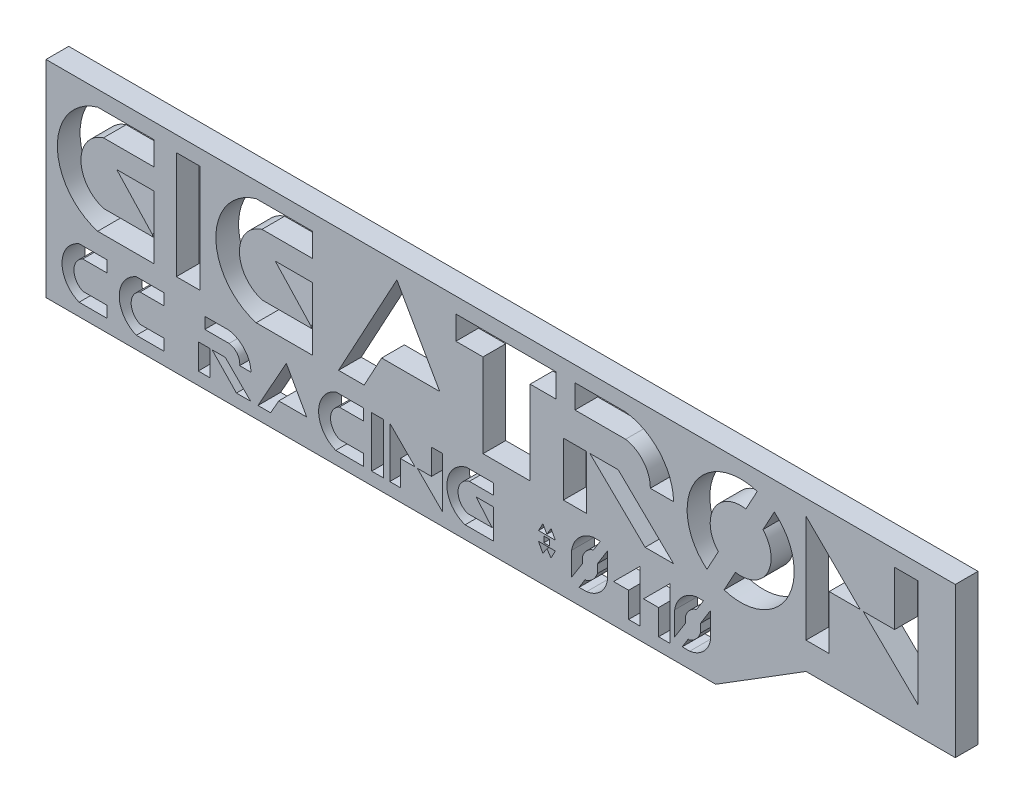
SolidWorks part; units mm, degrees
ref_plane "Front Plane" through (0, 0, 0) normal (0, 0, 1) x (1, 0, 0)
ref_plane "Top Plane" through (0, 0, 0) normal (0, 1, 0) x (1, 0, 0)
ref_plane "Right Plane" through (0, 0, 0) normal (1, 0, 0) x (0, 0, -1)
sketch "Sketch1" plane through (0, 0, 0) normal (0, 0, 1) x (1, 0, 0)
  line L0 (97.5, 52.5) -> (487.5, 52.5) construction
  line L1 (97.7035, 32.2566) -> (489.0368, 32.2566) construction
  line L2 (6.0369, 7.5244) -> (6.0369, 6.2034)
  line L3 (3.2137, 6.2034) -> (6.0369, 6.2034)
  line L4 (6.0369, 5.0366) -> (6.0369, 1.5154)
  line L5 (6.0369, 1.5154) -> (2.8899, 1.5154)
  line L6 (3.2137, 2.7845) -> (5.9435, 2.7845)
  line L7 (3.9568, 5.0366) -> (5.9435, 2.896)
  line L8 (5.9435, 2.7845) -> (5.9435, 2.896)
  line L9 (3.9568, 5.0366) -> (6.0369, 5.0366)
  line L10 (2.8899, 7.5244) -> (6.0369, 7.5244)
  line L11 (7.2903, 7.5244) -> (7.2903, 1.5154)
  line L12 (7.2903, 1.5154) -> (8.6142, 1.5154)
  line L13 (8.6142, 1.5154) -> (8.6142, 7.5244)
  line L14 (8.6142, 7.5244) -> (7.2903, 7.5244)
  line L15 (12.0783, 2.7845) -> (14.8081, 2.7845)
  line L16 (11.7545, 7.5244) -> (14.9015, 7.5244)
  line L17 (14.9015, 7.5244) -> (14.9015, 6.2034)
  line L18 (12.8214, 5.0366) -> (14.9015, 5.0366)
  line L19 (12.0783, 6.2034) -> (14.9015, 6.2034)
  line L20 (14.9015, 1.5154) -> (11.7545, 1.5154)
  line L21 (14.8081, 2.7845) -> (14.8081, 2.896)
  line L22 (14.9015, 5.0366) -> (14.9015, 1.5154)
  line L23 (12.8214, 5.0366) -> (14.8081, 2.896)
  line L24 (16.36, 1.5154) -> (19.6219, 7.5244)
  line L25 (19.6219, 7.5244) -> (22.0222, 3.3181)
  line L26 (22.0222, 3.3181) -> (18.7718, 3.3181)
  line L27 (18.7718, 3.3181) -> (17.7932, 1.5154)
  line L28 (17.7932, 1.5154) -> (16.36, 1.5154)
  line L29 (22.9223, 6.2034) -> (22.9223, 7.5244)
  line L30 (22.9223, 7.5244) -> (28.5231, 7.5244)
  line L31 (28.5231, 7.5244) -> (28.5231, 6.2034)
  line L32 (28.5231, 6.2034) -> (27.0784, 6.2034)
  line L33 (27.0784, 6.2034) -> (27.0784, 1.5154)
  line L34 (27.0784, 1.5154) -> (24.4392, 1.5154)
  line L35 (24.4392, 1.5154) -> (24.4392, 6.2034)
  line L36 (24.4392, 6.2034) -> (22.9223, 6.2034)
  line L37 (28.9324, 1.5154) -> (28.9324, 4.5199)
  line L38 (0, 8.3917) -> (50.8536, 8.3917)
  line L39 (0, 8.3917) -> (0, -3.145)
  line L40 (0, -3.145) -> (37.4561, -3.145)
  line L41 (50.8536, 8.3917) -> (50.8536, 0)
  line L42 (28.9324, 4.5199) -> (30.2353, 4.5199)
  line L43 (30.2353, 4.5199) -> (30.2353, 1.5154)
  line L44 (30.2353, 1.5154) -> (28.9324, 1.5154)
  line L45 (30.4133, 4.5199) -> (33.506, 1.5154)
  line L46 (33.506, 1.5154) -> (35.0989, 1.5154)
  line L47 (35.0989, 1.5154) -> (32.0062, 4.5199)
  line L48 (32.0062, 4.5199) -> (30.4133, 4.5199)
  line L49 (29.5839, 7.5244) -> (29.5839, 6.2034)
  line L50 (29.5839, 6.2034) -> (32.4138, 6.2034)
  line L51 (32.4138, 6.2034) -> (32.4138, 7.5244) construction
  line L52 (32.4138, 7.5244) -> (29.5839, 7.5244)
  line L53 (33.7966, 4.5199) -> (35.0992, 4.5199)
  line L54 (48.7766, 1.5154) -> (45.7105, 4.509)
  line L55 (45.7105, 4.509) -> (47.4627, 4.509)
  line L56 (47.4627, 4.509) -> (47.4627, 7.5244)
  line L57 (47.4627, 7.5244) -> (48.7766, 7.5244)
  line L58 (48.7766, 7.5244) -> (48.7766, 1.5154)
  line L59 (42.5034, 7.5244) -> (42.5034, 1.5154)
  line L60 (42.5034, 1.5154) -> (43.799, 1.5154)
  line L61 (43.799, 1.5154) -> (43.799, 4.5199)
  line L62 (43.799, 4.5199) -> (45.5406, 4.5199)
  line L63 (45.5406, 4.5199) -> (42.5034, 7.5244)
  line L64 (37.4561, -3.145) -> (42.5034, 0)
  line L65 (42.5034, 0) -> (50.8536, 0)
  line L66 (1.8512, 0.3925) -> (3.4007, 0.3925)
  line L67 (3.4007, 0.3925) -> (3.4007, -0.2437)
  line L68 (3.4007, -0.2437) -> (2.0566, -0.2437)
  line L69 (2.0638, -1.8089) -> (3.4007, -1.8089)
  line L70 (3.4007, -1.8089) -> (3.4007, -2.4417)
  line L71 (3.4007, -2.4417) -> (1.8512, -2.4417)
  line L72 (6.6011, -1.8089) -> (6.6011, -2.4417)
  line L73 (5.0516, 0.3925) -> (6.6011, 0.3925)
  line L74 (6.6011, -2.4417) -> (5.0516, -2.4417)
  line L75 (5.2642, -1.8089) -> (6.6011, -1.8089)
  line L76 (6.6011, -0.2437) -> (5.257, -0.2437)
  line L77 (6.6011, 0.3925) -> (6.6011, -0.2437)
  line L78 (17.7517, -0.2437) -> (16.4076, -0.2437)
  line L79 (16.4148, -1.8089) -> (17.7517, -1.8089)
  line L80 (17.7517, -2.4417) -> (16.2022, -2.4417)
  line L81 (16.2022, 0.3925) -> (17.7517, 0.3925)
  line L82 (17.7517, -1.8089) -> (17.7517, -2.4417)
  line L83 (17.7517, 0.3925) -> (17.7517, -0.2437)
  line L84 (30.0042, -1.728) -> (30.0042, -0.6842)
  line L85 (29.3957, -2.2683) -> (29.3957, -0.6842)
  line L86 (30.8351, -0.061) -> (30.8351, -1.0945)
  line L87 (31.4055, 0.5528) -> (31.4055, -1.0945)
  line L88 (29.3957, -2.2683) -> (30.2353, -2.2683)
  line L89 (30.5998, 0.5528) -> (31.4055, 0.5528)
  line L90 (30.8351, -0.061) -> (30.5998, -0.061)
  line L91 (30.0042, -1.728) -> (30.2353, -1.728)
  line L92 (35.1615, -2.2683) -> (35.1615, -0.6842)
  line L93 (35.1615, -2.2683) -> (36.0011, -2.2683)
  line L94 (36.6009, -0.061) -> (36.3656, -0.061)
  line L95 (36.3656, 0.5528) -> (37.1713, 0.5528)
  line L96 (36.6009, -0.061) -> (36.6009, -1.0945)
  line L97 (37.1713, 0.5528) -> (37.1713, -1.0945)
  line L98 (35.77, -1.728) -> (35.77, -0.6842)
  line L99 (35.77, -1.728) -> (36.0011, -1.728)
  line L100 (31.7414, -1.0246) -> (33.2093, 0.4432)
  line L101 (33.2093, 0.4432) -> (33.2093, -2.4417)
  line L102 (33.2093, -2.4417) -> (32.583, -2.4417)
  line L103 (32.583, -2.4417) -> (32.583, -1.0246)
  line L104 (32.583, -1.0246) -> (31.7414, -1.0246)
  line L105 (34.8857, 0.4432) -> (34.8857, -2.4417)
  line L106 (34.8857, -2.4417) -> (34.2594, -2.4417)
  line L107 (34.2594, -1.0246) -> (33.4178, -1.0246)
  line L108 (33.4178, -1.0246) -> (34.8857, 0.4432)
  line L109 (34.2594, -2.4417) -> (34.2594, -1.0246)
  line L110 (27.5415, -1.1748) -> (28.4841, -1.1748)
  line L111 (28.4841, -1.1748) -> (28.2445, -1.6381)
  line L112 (28.2445, -1.6381) -> (28.0128, -1.2946)
  line L113 (28.0128, -1.2946) -> (27.7891, -1.6381)
  line L114 (27.7891, -1.6381) -> (27.5415, -1.1748)
  line L115 (27.5415, -0.6528) -> (27.7891, -0.204)
  line L116 (27.845, -0.7682) -> (28.1646, -0.7682)
  line L117 (27.845, -0.7682) -> (27.845, -1.0945)
  line L118 (27.845, -1.0945) -> (28.1646, -1.0945)
  line L119 (28.1646, -0.7682) -> (28.1646, -1.0945)
  line L120 (27.7891, -0.204) -> (28.0128, -0.6012)
  line L121 (28.0128, -0.6012) -> (28.2445, -0.204)
  line L122 (28.2445, -0.204) -> (28.4841, -0.6528)
  line L123 (28.4841, -0.6528) -> (27.5415, -0.6528)
  line L124 (11.8532, -2.4417) -> (13.4413, 0.3925)
  line L125 (13.4413, 0.3925) -> (14.5821, -1.6381)
  line L126 (14.5821, -1.6381) -> (13.0149, -1.6381)
  line L127 (13.0149, -1.6381) -> (12.5646, -2.4417)
  line L128 (12.5646, -2.4417) -> (11.8532, -2.4417)
  line L129 (10.2382, -0.2437) -> (8.8784, -0.2437)
  line L130 (8.8784, -0.2437) -> (8.8784, 0.3925)
  line L131 (8.8784, 0.3925) -> (10.2382, 0.3925)
  line L132 (8.5152, -1.0246) -> (9.1703, -1.0246)
  line L133 (9.1703, -1.0246) -> (9.1703, -2.4417)
  line L134 (9.1703, -2.4417) -> (8.5152, -2.4417)
  line L135 (8.5152, -2.4417) -> (8.5152, -1.0246)
  line L136 (9.2871, -1.0246) -> (10.0265, -1.0246)
  line L137 (10.0265, -1.0246) -> (11.4436, -2.4417)
  line L138 (11.4436, -2.4417) -> (10.6492, -2.4417)
  line L139 (10.6492, -2.4417) -> (9.2871, -1.0246)
  line L140 (19.2254, 0.3925) -> (20.6425, -1.0246)
  line L141 (18.2123, 0.3925) -> (18.8636, 0.3925)
  line L142 (18.2123, 0.3925) -> (18.2123, -2.4417)
  line L143 (18.2123, -2.4417) -> (18.8636, -2.4417)
  line L144 (18.8636, 0.3925) -> (18.8636, -2.4417)
  line L145 (20.6425, -1.0246) -> (19.8134, -1.0246)
  line L146 (19.8134, -1.0246) -> (19.8134, -2.4417)
  line L147 (19.8134, -2.4417) -> (19.2254, -2.4417)
  line L148 (19.2254, -2.4417) -> (19.2254, 0.3925)
  line L149 (21.5592, 0.395) -> (22.1834, 0.395)
  line L150 (22.1834, 0.395) -> (22.1834, -2.4417)
  line L151 (22.1834, -2.4417) -> (20.7663, -1.0246)
  line L152 (20.7663, -1.0246) -> (21.5592, -1.0246)
  line L153 (21.5592, -1.0246) -> (21.5592, 0.395)
  line L154 (23.5035, 0.395) -> (25.0327, 0.395)
  line L155 (25.0327, 0.395) -> (25.0327, -0.204)
  line L156 (25.0327, -0.204) -> (23.6759, -0.204)
  line L157 (23.5674, -1.8089) -> (24.9423, -1.8089)
  line L158 (24.9423, -1.8089) -> (24.0558, -0.7682)
  line L159 (24.0558, -0.7682) -> (25.0327, -0.7682)
  line L160 (25.0327, -0.7682) -> (25.0327, -2.4257)
  line L161 (25.0327, -2.4257) -> (23.4406, -2.4257)
  line L162 (10.8306, -1.0246) -> (11.4643, -1.0246)
  arc A0 (2.8899, 7.5244) -> (2.8899, 1.5154) centre (3.7643, 4.5199) ccw
  arc A1 (3.2137, 6.2034) -> (3.2137, 2.7845) centre (3.7442, 4.494) ccw
  arc A2 (11.7545, 7.5244) -> (11.7545, 1.5154) centre (12.6289, 4.5199) ccw
  arc A3 (12.0783, 6.2034) -> (12.0783, 2.7845) centre (12.6088, 4.494) ccw
  arc A4 (32.4138, 6.2034) -> (33.7966, 4.5199) centre (32.1192, 4.5519) cw
  arc A5 (32.4138, 7.5244) -> (35.0992, 4.5199) centre (32.0158, 4.4663) cw
  circle A6 centre (38.8497, 4.509) radius 1.7044
  circle A7 centre (38.8497, 4.509) radius 2.9936
  arc A8 (1.8512, 0.3925) -> (1.8512, -2.4417) centre (2.4253, -1.0246) ccw
  arc A9 (2.0566, -0.2437) -> (2.0638, -1.8089) centre (2.4253, -1.0246) ccw
  arc A10 (5.0516, 0.3925) -> (5.0516, -2.4417) centre (5.6257, -1.0246) ccw
  arc A11 (5.257, -0.2437) -> (5.2642, -1.8089) centre (5.6257, -1.0246) ccw
  arc A12 (16.4076, -0.2437) -> (16.4148, -1.8089) centre (16.7763, -1.0246) ccw
  arc A13 (16.2022, 0.3925) -> (16.2022, -2.4417) centre (16.7763, -1.0246) ccw
  arc A14 (29.3957, -0.6842) -> (30.5998, 0.5528) centre (30.8661, -0.9109) cw
  arc A15 (30.0042, -0.6842) -> (30.5998, -0.061) centre (30.8989, -0.943) cw
  arc A16 (30.8351, -1.0945) -> (30.2353, -1.728) centre (29.8559, -0.7682) cw
  arc A17 (31.4055, -1.0945) -> (30.2353, -2.2683) centre (30.0493, -0.9128) cw
  arc A18 (35.77, -0.6842) -> (36.3656, -0.061) centre (36.6647, -0.943) cw
  arc A19 (36.6009, -1.0945) -> (36.0011, -1.728) centre (35.6217, -0.7682) cw
  arc A20 (37.1713, -1.0945) -> (36.0011, -2.2683) centre (35.8151, -0.9128) cw
  arc A21 (35.1615, -0.6842) -> (36.3656, 0.5528) centre (36.6319, -0.9109) cw
  arc A22 (10.2382, 0.3925) -> (11.4643, -1.0246) centre (9.9864, -1.0644) cw
  arc A23 (10.2382, -0.2437) -> (10.8306, -1.0246) centre (10.1439, -0.9304) cw
  arc A24 (23.5035, 0.395) -> (23.4406, -2.4257) centre (23.8923, -1.0248) ccw
  arc A25 (23.6759, -0.204) -> (23.5674, -1.8089) centre (23.8923, -1.0248) ccw
extrude "Boss-Extrude1" add sketch "Sketch1" along normal blind 1.27 contours L64 L65 L41 L38 L39 L40 A23 L129 L130 L131 A22 L162 L87 A17 L88 L85 A14 L89 A13 L81 L83 L78 A12 L79 L82 L80 A7 L57 L58 L54 L55 L56 L43 L44 L37 L42 L35 L36 L29 L30 L31 L32 L33 L34
sketch "Sketch2" plane through (0, 0, 1.27) normal (0, 0, 1) x (1, 0, 0)
  line L0 (29.3957, -1.9921) -> (30.0042, -1.0284)
  line L1 (29.3957, -2.2683) -> (29.3957, -0.6842) construction
  line L2 (30.5998, 0.5528) -> (31.4055, 0.5528) construction
  line L3 (31.0026, 0.5528) -> (31.4055, 0.5528)
  line L4 (31.4055, 0.5528) -> (31.4055, -1.0945) construction
  line L5 (31.4055, 0.2984) -> (30.8351, -0.6223)
  line L6 (29.3957, -2.2683) -> (30.2353, -2.2683) construction
  line L7 (29.8155, -2.2683) -> (29.3957, -2.2683)
  line L8 (29.3957, -2.2683) -> (29.3957, -1.9921)
  line L9 (31.4055, 0.5528) -> (31.4055, 0.2984)
  line L10 (36.8513, 1.9677) -> (37.8075, 1.4487)
  line L11 (36.8513, 1.9677) -> (37.601, 3.3489)
  line L12 (37.8075, 1.4487) -> (38.5572, 2.8298)
  line L13 (39.892, 7.5693) -> (40.8482, 7.0502)
  line L14 (36.8513, 1.9677) -> (40.8482, 7.0502) construction
  line L15 (37.8075, 1.4487) -> (39.892, 7.5693) construction
  line L16 (30.0042, -1.728) -> (30.0042, -0.6842) construction
  line L17 (16.36, 1.5154) -> (19.6219, 7.5244) construction
  line L18 (35.5813, -2.2683) -> (35.916, -1.728)
  line L19 (35.1615, -2.2683) -> (36.0011, -2.2683) construction
  line L20 (37.1713, 0.5528) -> (37.1713, -1.0945) construction
  line L21 (37.1713, 0.2984) -> (37.1713, 0.5528)
  line L22 (37.1713, 0.5528) -> (36.7684, 0.5528)
  line L23 (36.3656, 0.5528) -> (37.1713, 0.5528) construction
  line L24 (36.7684, 0.5528) -> (36.3809, -0.061)
  line L25 (35.1615, -2.2683) -> (35.1615, -0.6842) construction
  line L26 (35.1615, -1.9921) -> (35.1615, -2.2683)
  line L27 (35.1615, -2.2683) -> (35.5813, -2.2683)
  line L28 (30.8351, -0.061) -> (30.5998, -0.061) construction
  line L29 (30.8351, -0.061) -> (30.8351, -1.0945) construction
  line L30 (30.0042, -1.728) -> (30.2353, -1.728) construction
  line L31 (35.77, -1.728) -> (35.77, -0.6842) construction
  line L32 (35.77, -1.728) -> (36.0011, -1.728) construction
  line L33 (36.6009, -0.061) -> (36.3656, -0.061) construction
  line L34 (36.6009, -0.061) -> (36.6009, -1.0945) construction
  line L35 (30.0042, -1.0284) -> (30.0042, -0.6842)
  line L36 (30.6151, -0.061) -> (30.5998, -0.061)
  line L37 (30.8351, -0.6223) -> (30.8351, -1.0945)
  line L38 (30.1502, -1.728) -> (30.2353, -1.728)
  line L39 (35.77, -1.0284) -> (35.77, -0.6842)
  line L40 (35.916, -1.728) -> (36.0011, -1.728)
  line L41 (36.3809, -0.061) -> (36.3656, -0.061)
  line L42 (36.6009, -0.6223) -> (36.6009, -1.0945)
  line L43 (40.0984, 5.669) -> (40.8482, 7.0502)
  line L44 (39.1422, 6.1881) -> (39.892, 7.5693)
  line L45 (35.77, -1.0284) -> (35.1615, -1.9921)
  line L46 (36.6009, -0.6223) -> (37.1713, 0.2984)
  line L47 (30.1502, -1.728) -> (29.8155, -2.2683)
  line L48 (30.6151, -0.061) -> (31.0026, 0.5528)
  circle A0 centre (38.8497, 4.509) radius 2.9936 construction
  circle A1 centre (38.8497, 4.509) radius 1.7044 construction
  arc A2 (38.5572, 2.8298) -> (40.0984, 5.669) centre (38.8497, 4.509) ccw
  arc A3 (30.5998, -0.061) -> (30.0042, -0.6842) centre (30.8989, -0.943) ccw construction
  arc A4 (30.2353, -1.728) -> (30.8351, -1.0945) centre (29.8559, -0.7682) ccw construction
  arc A5 (36.0011, -1.728) -> (36.6009, -1.0945) centre (35.6217, -0.7682) ccw construction
  arc A6 (36.3656, -0.061) -> (35.77, -0.6842) centre (36.6647, -0.943) ccw construction
  arc A7 (30.5998, -0.061) -> (30.0042, -0.6842) centre (30.8989, -0.943) ccw
  arc A8 (30.2353, -1.728) -> (30.8351, -1.0945) centre (29.8559, -0.7682) ccw
  arc A9 (36.0011, -1.728) -> (36.6009, -1.0945) centre (35.6217, -0.7682) ccw
  arc A10 (36.3656, -0.061) -> (35.77, -0.6842) centre (36.6647, -0.943) ccw
  arc A11 (39.1422, 6.1881) -> (37.601, 3.3489) centre (38.8497, 4.509) ccw
  point P17 (38.8497, 4.509)
extrude "Boss-Extrude2" add sketch "Sketch2" against normal up to surface (1.27 mm away) up to face at (10.1572, -0.235, 0)
